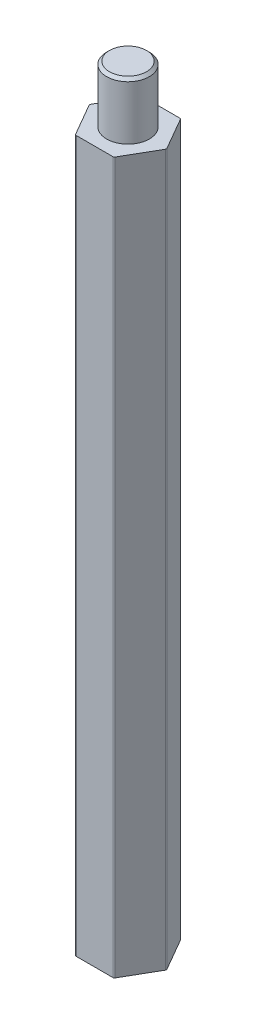
SolidWorks part; units mm, degrees
material "黄铜"
ref_plane "前视基准面" through (0, 0, 0) normal (0, 0, 1) x (1, 0, 0)
ref_plane "上视基准面" through (0, 0, 0) normal (0, 1, 0) x (1, 0, 0)
ref_plane "右视基准面" through (0, 0, 0) normal (1, 0, 0) x (0, 0, -1)
sketch "草图1" plane through (0, 0, 0) normal (0, 1, 0) x (1, 0, 0)
  line L1 (2.7135, 0) -> (1.3568, 2.35)
  line L2 (1.3568, 2.35) -> (-1.3568, 2.35)
  line L3 (-1.3568, 2.35) -> (-2.7135, 0)
  line L4 (-2.7135, 0) -> (-1.3568, -2.35)
  line L5 (-1.3568, -2.35) -> (1.3568, -2.35)
  line L6 (1.3568, -2.35) -> (2.7135, 0)
  circle A0 centre (0, 0) radius 2.35 construction
  dimension "D1" = 4.7
extrude "凸台-拉伸1" add sketch "草图1" along normal blind 50
sketch "草图2" plane through (0, 50, 0) normal (0, 1, 0) x (1, 0, 0)
  circle A0 centre (0, 0) radius 1.5
  dimension "D1" = 3
extrude "凸台-拉伸2" add sketch "草图2" along normal blind 4
cosmetic thread "装饰螺纹线1" parameters "D2"=2.459
sketch "草图3" plane through (0, 0, 0) normal (0, -1, 0) x (1, 0, 0)
  circle A0 centre (0, 0) radius 1.5
  dimension "D1" = 3
extrude "切除-拉伸1" cut sketch "草图3" against normal blind 4
cosmetic thread "装饰螺纹线2" parameters "D2"=4
chamfer "倒角1" distance 0.2 angle 45
fillet "圆角1" radius 0.1
